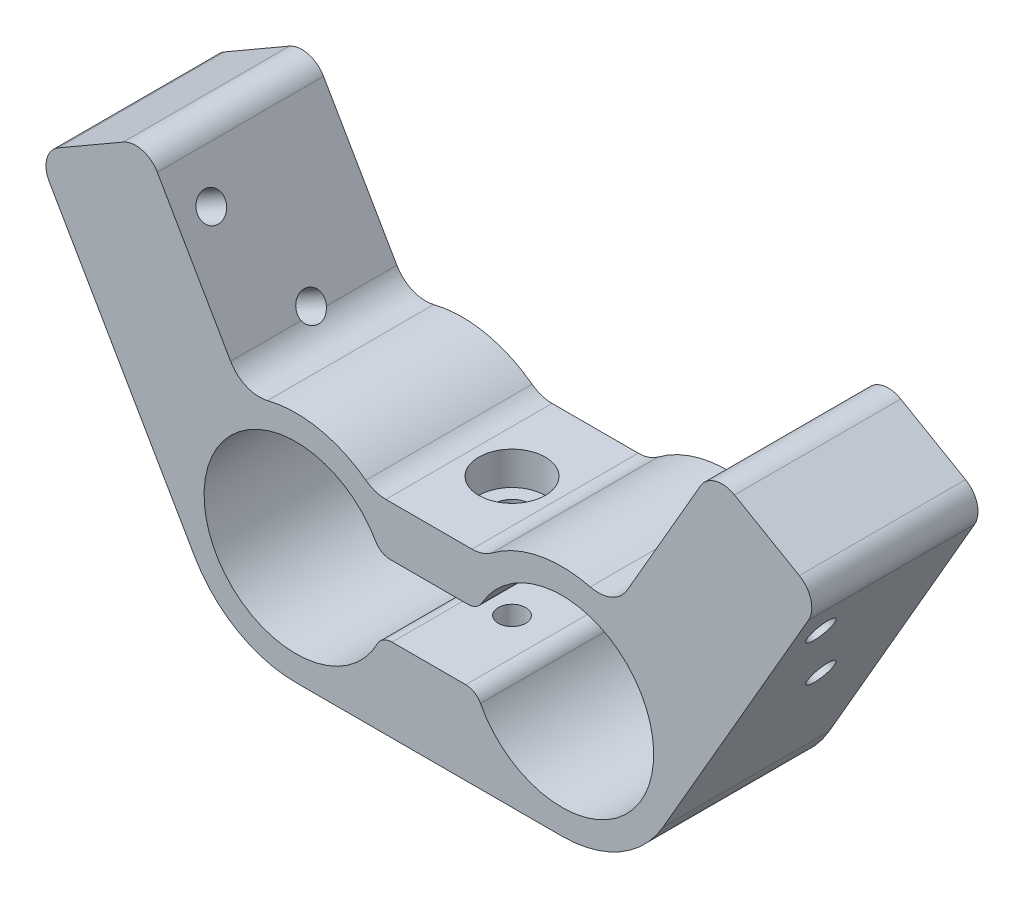
SolidWorks part; units mm, degrees
material "Сплав 2024"
ref_plane "Спереди" through (0, 0, 0) normal (0, 0, 1) x (1, 0, 0)
ref_plane "Сверху" through (0, 0, 0) normal (0, 1, 0) x (1, 0, 0)
ref_plane "Справа" through (0, 0, 0) normal (1, 0, 0) x (0, 0, -1)
sketch "Эскиз1" plane through (0, 0, 0) normal (0, 0, 1) x (1, 0, 0)
  line L0 (-97.2999, 0) -> (107.2229, 0) construction
  line L1 (0, 45.7486) -> (0, -47.2091) construction
  line L2 (-6.6085, 10.45) -> (6.6085, 10.45)
  line L3 (-5.8857, 4.45) -> (5.8857, 4.45)
  line L4 (47.1677, 25.884) -> (28.1677, -7.025)
  line L5 (-47.1677, 25.884) -> (-28.1677, -7.025)
  line L6 (-34.1773, 33.384) -> (-22.1862, 12.6148)
  line L7 (34.1773, 33.384) -> (22.1862, 12.6148)
  line L8 (-47.1677, 25.884) -> (-34.1773, 33.384)
  line L9 (34.1773, 33.384) -> (47.1677, 25.884)
  line L10 (-16, -14.05) -> (16, -14.05)
  line L11 (-5.7189, -4.05) -> (5.7189, -4.05)
  arc A0 (-5.8857, 4.45) -> (-5.7189, -4.05) centre (-16, 0) ccw
  arc A1 (5.7189, -4.05) -> (5.8857, 4.45) centre (16, 0) ccw
  arc A2 (-6.6085, 10.45) -> (-22.1862, 12.6148) centre (-16, 0) ccw
  arc A3 (-28.1677, -7.025) -> (-16, -14.05) centre (-16, 0) ccw
  arc A4 (16, -14.05) -> (28.1677, -7.025) centre (16, 0) ccw
  circle A5 centre (-16, 0) radius 14.05 construction
  arc A6 (22.1862, 12.6148) -> (6.6085, 10.45) centre (16, 0) ccw
  circle A7 centre (-16, 0) radius 11.05 construction
  circle A8 centre (16, 0) radius 14.05 construction
  circle A9 centre (16, 0) radius 11.05 construction
  point P5 (0, 0)
  point P8 (30, 0)
  point P9 (16.035, -0.0857)
  point P10 (-5.4806, 3.2161)
  point P29 (-2, 0)
  point P32 (26.5672, 3.2307)
  point P33 (30.05, 0)
  point P36 (26.5194, 3.2161)
  dimension "D1" = 22.1
  dimension "D2" = 16
  dimension "D6" = 3
  dimension "D4" = 22.1
  dimension "D3" = 16
  dimension "D7" = 6
  dimension "D8" = 30
  dimension "D9" = 30
  dimension "D10" = 15
  dimension "D11" = 15
  dimension "D12" = 10
  dimension "D13" = 8.5
  dimension "D14" = 38
  dimension "D15" = 38
  dimension "D5" = 3
extrude "Бобышка-Вытянуть2" add sketch "Эскиз1" along normal blind 20
sketch "Эскиз3" plane through (0, 10.45, 0) normal (0, 1, 0) x (1, 0, 0)
  line L0 (0, 0) -> (0, -20) construction
  line L1 (6.6085, -20) -> (-6.6085, -20) construction
  line L2 (6.6085, -10) -> (-6.6085, -10) construction
  line L4 (-6.6085, -20) -> (-6.6085, 0) construction
  line L5 (6.6085, -20) -> (6.6085, 0) construction
hole_wizard "Цековка для винта с внутренним шестигранником M41" positions "Эскиз5" profile "Эскиз4" counterbore size "M4" standard "Ansi Metric" end condition up to next
sketch "Эскиз5" plane through (0, 10.45, 0) normal (0, 1, 0) x (1, 0, 0)
  line L0 (0, 0) -> (0, -20) construction
  point P0 (0, -10)
sketch "Эскиз4" plane through (0, 10.45, 10) normal (1, 0, 0) x (0, 0, 1)
  line L0 (0, 0) -> (0, 6)
  line L1 (0, 6) -> (2.25, 6)
  line L3 (2.25, 6) -> (2.25, 4)
  line L4 (2.25, 4) -> (4, 4)
  line L5 (4, 4) -> (4, 0)
  line L7 (4, 0) -> (0, 0)
  line L11 (0, -6.35) -> (0, 107.95) construction
  dimension "Диаметр сквозного отверстия" = 4.5
  dimension "Глубина сквозного отверстия" = 6
  dimension "Диаметр цековки" = 8
  dimension "Глубина цековки" = 4
hole_wizard "Отверстие обработанное метчиком M4x0.71" positions "Эскиз7" profile "Эскиз6" tap size "M4x0.7" standard "Ansi Metric" end condition through all
sketch "Эскиз7" plane through (0, -4.05, 0) normal (0, 1, 0) x (1, 0, 0)
  line L0 (0, 0) -> (0, -20) construction
  point P0 (0, -10)
sketch "Эскиз6" plane through (0, -4.05, 10) normal (1, 0, 0) x (0, 0, 1)
  line L0 (0, 0) -> (0, 10)
  line L1 (0, 10) -> (1.65, 10)
  line L2 (1.65, 10) -> (1.65, 0)
  line L5 (1.65, 0) -> (0, 0)
  line L11 (0, -6.35) -> (0, 107.95) construction
  dimension "Диаметр проходного сверла" = 3.3
  dimension "Глубина проходного сверла" = 10
cosmetic thread "Отверстие резьбы1" parameters "D2"=4
ref_plane "Плоскость1" through (0, 0, 0) normal (-1, 0, 0) x (0, 0, 1)
fillet "Скругление1" radius 2 4 edges at (-5.7189, -4.05, 10) (5.7189, -4.05, 10) (5.8857, 4.45, 10) (-5.8857, 4.45, 10)
fillet "Скругление2" radius 4 4 edges at (6.6085, 10.45, 10) (-22.1862, 12.6148, 10) (-6.6085, 10.45, 10) (22.1862, 12.6148, 10)
sketch "Эскиз8" plane through (24.1677, -13.9532, 0) normal (0.866, -0.5, 0) x (0, 0, -1)
  line L0 (-10, 46) -> (-10, 8) construction
  line L1 (-20, 46) -> (0, 46) construction
  line L2 (-20, 8) -> (0, 8) construction
  line L3 (-16, 46) -> (-16, 8) construction
  line L4 (-20, 8) -> (-20, 46) construction
  line L5 (-20, 38) -> (0, 38) construction
  line L6 (0, 8) -> (0, 46) construction
  line L7 (0, 26) -> (-20, 26) construction
  dimension "D1" = 4
  dimension "D2" = 8
  dimension "D3" = 12
hole_wizard "Отверстие обработанное метчиком M4x0.72" positions "Эскиз10" profile "Эскиз9" tap size "M4x0.7" standard "Ansi Metric" end condition through all
sketch "Эскиз10" plane through (24.1677, -13.9532, 0) normal (0.866, -0.5, 0) x (0, 0, -1)
  line L0 (-10, 46) -> (-10, 8) construction
  line L1 (0, 26) -> (-20, 26) construction
  line L2 (-20, 38) -> (0, 38) construction
  line L3 (-16, 46) -> (-16, 8) construction
  point P0 (-10, 26)
  point P2 (-16, 38)
sketch "Эскиз9" plane through (37.1677, 8.5635, 10) normal (0, 0, 1) x (0.5, 0.866, 0)
  line L0 (0, 0) -> (0, 85.4468)
  line L1 (0, 85.4468) -> (1.65, 85.4468)
  line L2 (1.65, 85.4468) -> (1.65, 0)
  line L5 (1.65, 0) -> (0, 0)
  line L11 (0, -6.35) -> (0, 107.95) construction
  dimension "Диаметр проходного сверла" = 3.3
  dimension "Глубина проходного сверла" = 85.4468
cosmetic thread "Отверстие резьбы2" parameters "D2"=4
cosmetic thread "Отверстие резьбы3" parameters "D2"=4
ref_plane "Плоскость2" through (0, 0, 0) normal (1, 0, 0) x (0, 0, -1)
mirror "Зеркальное отражение1" about plane through (0, 0, 0) normal (1, 0, 0) of "Отверстие обработанное метчиком M4x0.72"
fillet "Скругление3" radius 3 4 edges at (47.1677, 25.884, 10) (34.1773, 33.384, 10) (-34.1773, 33.384, 10) (-47.1677, 25.884, 10)
